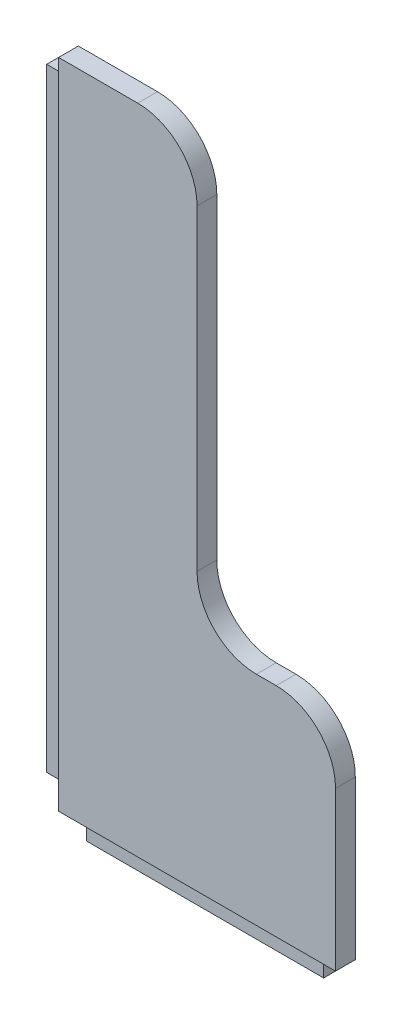
SolidWorks part; units mm, degrees
ref_plane "Alzado" through (0, 0, 0) normal (0, 0, 1) x (1, 0, 0)
ref_plane "Planta" through (0, 0, 0) normal (0, 1, 0) x (1, 0, 0)
ref_plane "Vista lateral" through (0, 0, 0) normal (1, 0, 0) x (0, 0, -1)
sketch "Croquis2" plane through (0, 0, 0) normal (0, 0, 1) x (1, 0, 0)
  line L6 (0, 0) -> (6.35, 0)
  line L7 (0, 0) -> (0, 6.35)
  line L8 (0, 6.35) -> (-6.35, 6.35)
  line L9 (6.35, 0) -> (6.35, -6.35)
  line L10 (6.35, -6.35) -> (82.55, -6.35)
  line L11 (-6.35, 6.35) -> (-6.35, 203.2)
  line L12 (82.55, -6.35) -> (82.55, 0)
  line L13 (82.55, 0) -> (88.9, 0)
  line L15 (-6.35, 203.2) -> (0, 203.2)
  line L16 (0, 203.2) -> (0, 209.55)
  line L17 (0, 209.55) -> (25.4, 209.55)
  line L18 (44.45, 190.5) -> (44.45, 88.9)
  line L19 (63.5, 69.85) -> (69.85, 69.85)
  line L20 (88.9, 50.8) -> (88.9, 0)
  arc A3 (25.4, 209.55) -> (44.45, 190.5) centre (25.4, 190.5) cw
  arc A4 (44.45, 88.9) -> (63.5, 69.85) centre (63.5, 88.9) ccw
  arc A5 (69.85, 69.85) -> (88.9, 50.8) centre (69.85, 50.8) cw
  point P21 (44.45, 209.55)
  point P24 (44.45, 69.85)
  dimension "D5" = 76.2
  dimension "D11" = 19.05
  dimension "D1" = 6.35
  dimension "D2" = 6.35
  dimension "D3" = 6.35
  dimension "D4" = 6.35
  dimension "D6" = 6.35
  dimension "D7" = 196.85
  dimension "D8" = 6.35
  dimension "D9" = 44.45
  dimension "D10" = 139.7
extrude "Saliente-Extruir3" add sketch "Croquis2" along normal blind 6.35
sketch "Croquis5" plane through (-6.35, 0, 0) normal (-1, 0, 0) x (0, 0, 1)
  line L0 (6.35, 6.35) -> (0, 6.35) construction
  line L1 (0, 203.2) -> (2.54, 203.2)
  line L2 (0, 203.2) -> (0, 6.35)
  line L3 (0, 6.35) -> (2.54, 6.35)
  line L4 (2.54, 203.2) -> (2.54, 6.35)
  dimension "D1" = 2.54
extrude "Cortar-Extruir1" cut sketch "Croquis5" against normal blind 6.35
move or copy body "Sólido-Mover/Copiar1" bodies to move or copy 103 copy no translate (-148.301, -44.9601, 222.609)
sketch "Croquis6" plane through (0, 0, 228.959) normal (0, 0, 1) x (1, 0, 0)
  line L1 (-154.651, 158.2399) -> (-148.301, 158.2399)
  line L2 (-154.651, 158.2399) -> (-154.651, -38.6101)
  line L3 (-154.651, -38.6101) -> (-148.301, -38.6101)
  line L4 (-148.301, 158.2399) -> (-148.301, -38.6101)
  line L5 (-141.951, -44.9601) -> (-65.751, -44.9601)
  line L6 (-141.951, -44.9601) -> (-141.951, -51.3101)
  line L7 (-141.951, -51.3101) -> (-65.751, -51.3101)
  line L8 (-65.751, -44.9601) -> (-65.751, -51.3101)
extrude "Cortar-Extruir2" cut sketch "Croquis6" against normal through all
sketch "Croquis7" plane through (-148.301, 0, 0) normal (-1, 0, 0) x (0, 0, 1)
  line L11 (222.609, 164.5899) -> (222.609, -44.9601) construction
  line L12 (222.609, -38.6101) -> (226.419, -38.6101)
  line L13 (222.609, -38.6101) -> (222.609, 158.2399)
  line L14 (222.609, 158.2399) -> (226.419, 158.2399)
  line L15 (226.419, -38.6101) -> (226.419, 158.2399)
  line L16 (228.959, -44.9601) -> (222.609, -44.9601) construction
  dimension "D1" = 6.35
  dimension "D2" = 3.81
  dimension "D3" = 196.85
extrude "Saliente-Extruir5" add sketch "Croquis7" along normal blind 6.35
sketch "Croquis8" plane through (0, -44.9601, 0) normal (0, -1, 0) x (-1, 0, 0)
  line L0 (148.301, -222.609) -> (59.401, -222.609) construction
  line L1 (141.951, -222.609) -> (65.751, -222.609)
  line L2 (141.951, -222.609) -> (141.951, -226.419)
  line L3 (141.951, -226.419) -> (65.751, -226.419)
  line L4 (65.751, -222.609) -> (65.751, -226.419)
  line L5 (148.301, -222.609) -> (148.301, -226.419) construction
  dimension "D1" = 6.35
  dimension "D2" = 3.81
  dimension "D3" = 76.2
extrude "Saliente-Extruir6" add sketch "Croquis8" along normal blind 6.35
